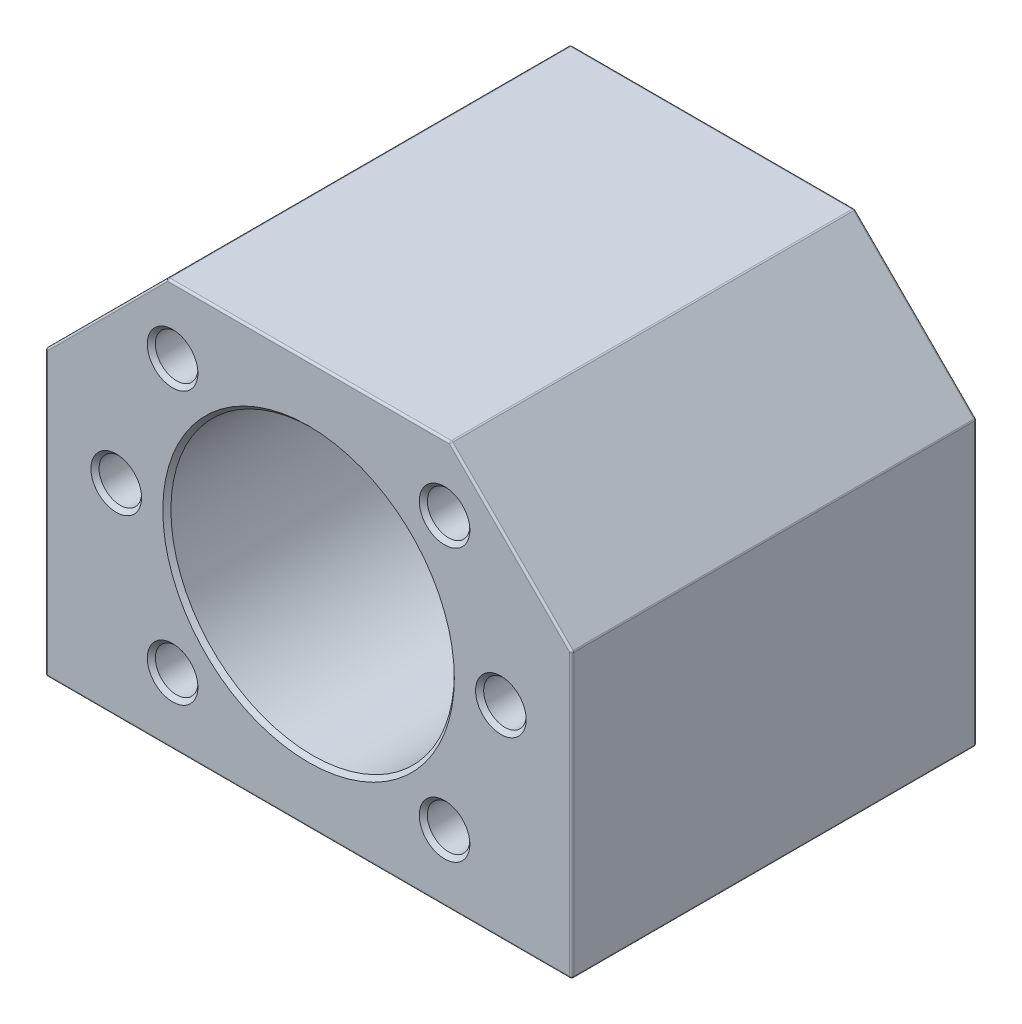
SolidWorks part; units mm, degrees
ref_plane "Plan de face" through (0, 0, 0) normal (0, 0, 1) x (1, 0, 0)
ref_plane "Plan de dessus" through (0, 0, 0) normal (0, 1, 0) x (1, 0, 0)
ref_plane "Plan de droite" through (0, 0, 0) normal (1, 0, 0) x (0, 0, -1)
sketch "Esquisse1" plane through (0, 0, 0) normal (0, 0, 1) x (1, 0, 0)
  line L1 (0, 0) -> (52, 0)
  line L2 (0, 0) -> (0, 40)
  line L3 (0, 40) -> (52, 40)
  line L4 (52, 0) -> (52, 40)
  circle A0 centre (26, 20) radius 14
extrude "Boss.-Extru.1" add sketch "Esquisse1" along normal blind 40
chamfer "Chanfrein1" distance 12 angle 45 2 edges at (0, 40, 20) (52, 40, 20)
hole_wizard "Trou taraudé M51" positions "Esquisse3" profile "Esquisse2" tap size "M5" standard "DIN"
sketch "Esquisse3" plane through (0, 0, 40) normal (0, 0, 1) x (1, 0, 0)
  line L0 (0, 0) -> (52, 0) construction
  line L1 (0, 28) -> (0, 0) construction
  point P0 (7, 20)
  point P2 (45, 20)
  dimension "D1" = 20
  dimension "D2" = 20
  dimension "D3" = 38
  dimension "D4" = 7
cosmetic thread "Filetage de perçage1" parameters "D1"=10, "D2"=5
cosmetic thread "Filetage de perçage2" parameters "D1"=10, "D2"=5
sketch "Esquisse2" plane through (7, 20, 40) normal (1, 0, 0) x (0, -1, 0)
  line L0 (0, 0) -> (0, 15.2618)
  line L1 (0, 15.2618) -> (2.1, 14)
  line L2 (2.1, 14) -> (2.1, 0)
  line L5 (2.1, 0) -> (0, 0)
  line L10 (0, 15.2618) -> (-2.1, 14) construction
  line L11 (0, -6.35) -> (0, 107.95) construction
  dimension "Diamètre du trou pour taraudage" = 4.2
  dimension "Profondeur du trou pour taraudage" = 14
  dimension "Angle de pointe" = 118
pattern_circular "Répétition circulaire1" count 2 every 45 about axis through (26, 20, 0) along (0, 0, 1) of "Trou taraudé M51"
pattern_circular "Répétition circulaire2" count 2 every 315 about axis through (26, 20, 0) along (0, 0, 1) of "Trou taraudé M51"
hole_wizard "Trou taraudé M52" positions "Esquisse5" profile "Esquisse4" tap size "M5" standard "DIN"
sketch "Esquisse5" plane through (0, 0, 0) normal (0, -1, 0) x (-1, 0, 0)
  line L0 (0, -40) -> (-52, -40) construction
  line L1 (0, -40) -> (0, 0) construction
  point P0 (-46, -32)
  point P2 (-46, -8)
  point P4 (-6, -32)
  point P6 (-6, -8)
  dimension "D1" = 8
  dimension "D2" = 24
  dimension "D3" = 40
  dimension "D4" = 6
  dimension "D5" = 6
  dimension "D6" = 24
  dimension "D7" = 40
  dimension "D8" = 8
sketch "Esquisse4" plane through (46, 0, 32) normal (1, 0, 0) x (0, 0, -1)
  line L0 (0, 0) -> (0, 15.2618)
  line L1 (0, 15.2618) -> (2.1, 14)
  line L2 (2.1, 14) -> (2.1, 0)
  line L5 (2.1, 0) -> (0, 0)
  line L10 (0, 15.2618) -> (-2.1, 14) construction
  line L11 (0, -6.35) -> (0, 107.95) construction
  dimension "Diamètre du trou pour taraudage" = 4.2
  dimension "Profondeur du trou pour taraudage" = 14
  dimension "Angle de pointe" = 118
cosmetic thread "Filetage de perçage3" parameters "D1"=10, "D2"=5
cosmetic thread "Filetage de perçage4" parameters "D1"=10, "D2"=5
cosmetic thread "Filetage de perçage5" parameters "D1"=10, "D2"=5
cosmetic thread "Filetage de perçage6" parameters "D1"=10, "D2"=5
fillet "Congé1" radius 0.2 19 edges at (52, 14, 0) (46, 34, 0) (26, 40, 0) (6, 34, 0) (0, 14, 0) (52, 28, 20) (40, 40, 20) (12, 40, 20) (0, 28, 20) (6, 34, 40) (26, 40, 40) (46, 34, 40) (52, 14, 40) (52, 0, 20) (26, 0, 0) (0, 14, 40) (0, 0, 20) (26, 0, 40) (40, 20, 0)
chamfer "Chanfrein2" distance 0.4 angle 45 7 edges at (41.535, 6.565, 40) (47.1, 20, 40) (41.535, 33.435, 40) (14.665, 33.435, 40) (9.1, 20, 40) (14.665, 6.565, 40) (40, 20, 40)
